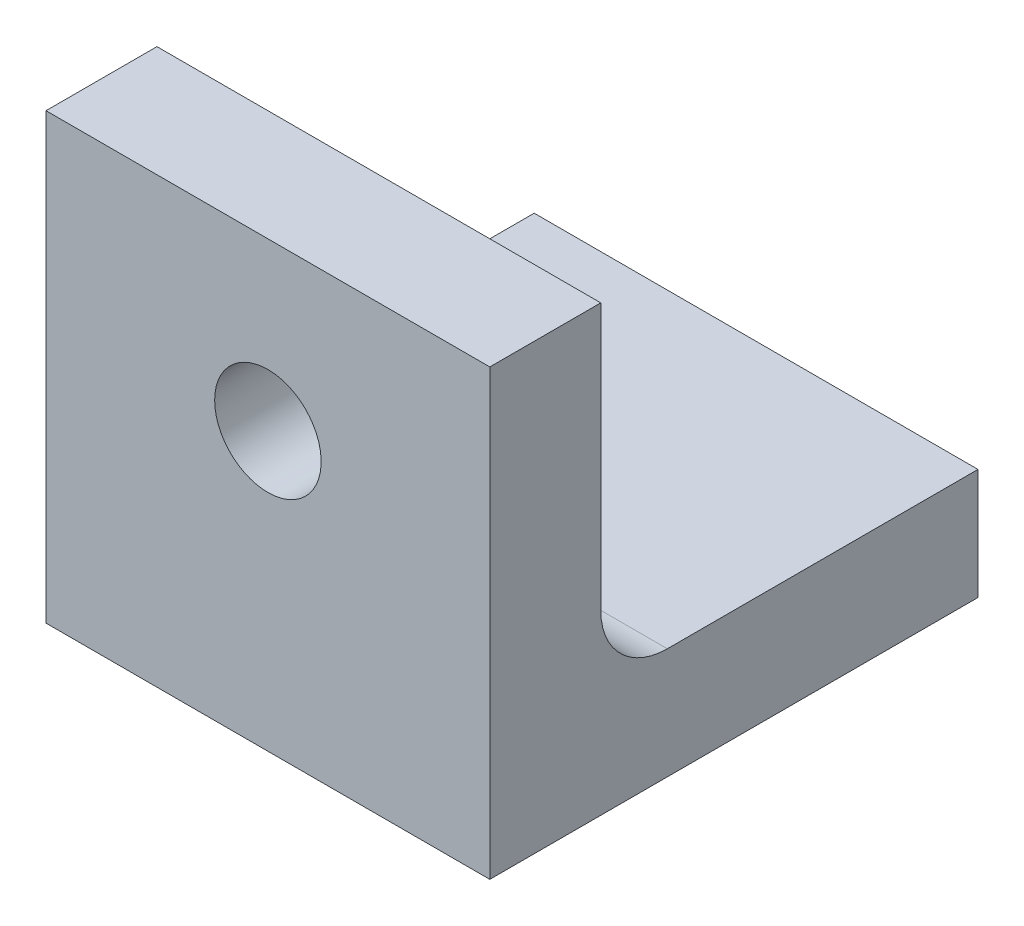
SolidWorks part; units mm, degrees
ref_plane "Front Plane" through (0, 0, 0) normal (0, 0, 1) x (1, 0, 0)
ref_plane "Top Plane" through (0, 0, 0) normal (0, 1, 0) x (1, 0, 0)
ref_plane "Right Plane" through (0, 0, 0) normal (1, 0, 0) x (0, 0, -1)
sketch "Sketch1" plane through (0, 0, 0) normal (0, 1, 0) x (1, 0, 0)
  line L0 (-10, 6) -> (10, 6)
  line L1 (-10, 11) -> (10, 11)
  line L2 (-10, 11) -> (-10, -11)
  line L3 (-10, -11) -> (10, -11)
  line L4 (10, 11) -> (10, -11)
  line L5 (-10, 11) -> (10, -11) construction
  line L6 (-10, -11) -> (10, 11) construction
  line L7 (-10, -6) -> (10, -6)
  point P0 (0, 0)
  dimension "D1" = 20
  dimension "D2" = 22
  dimension "D3" = 5
  dimension "D4" = 5
extrude "Boss-Extrude1" add sketch "Sketch1" along normal blind 5 contours L4 L1 L2 L0 | L2 L7 L4 L0 | L7 L2 L3 L4
sketch "Sketch2" plane through (0, 0, 11) normal (0, 0, 1) x (1, 0, 0)
  line L2 (10, 5) -> (-10, 5)
  line L3 (-10, 5) -> (-10, 0) construction
  line L5 (10, 5) -> (10, 20)
  line L6 (10, 20) -> (-10, 20)
  line L7 (-10, 5) -> (-10, 20)
  line L8 (-10, 5) -> (10, 5) construction
  point P1 (0, 0)
  point P9 (0, 0)
  point P10 (-10, 9.3459)
  dimension "D1" = 15
extrude "Boss-Extrude2" add sketch "Sketch2" along a picked direction on the side against the normal blind 5
hole_wizard "Ø5.0 (5) Diameter Hole1" positions "Sketch3" profile "Sketch4" hole size "Ø5.0" standard "ANSI Metric" end condition up to next
sketch "Sketch3" plane through (0, 5, 0) normal (0, 1, 0) x (1, 0, 0)
  point P0 (0, 0)
sketch "Sketch4" plane through (0, 5, 0) normal (1, 0, 0) x (0, 0, 1)
  line L0 (0, 0) -> (0, 5)
  line L1 (0, 5) -> (2.5, 5)
  line L2 (2.5, 5) -> (2.5, 0)
  line L5 (2.5, 0) -> (0, 0)
  line L11 (0, -6.35) -> (0, 107.95) construction
  dimension "Thru Hole Dia." = 5
  dimension "Thru Hole Depth" = 5
sketch "Sketch7" plane through (0, 0, 6) normal (0, 0, 1) x (1, 0, 0)
  line L3 (10, 5) -> (10, 20) construction
  line L4 (10, 20) -> (-10, 20) construction
  point P0 (0, 12.5)
  point P8 (0, 0)
  point P10 (10, 17.0161)
  point P11 (10, 14.4031)
  point P12 (0, 0)
  point P13 (0, 0)
  point P14 (10, 0)
  point P16 (10, 20)
  point P21 (10, 12.5)
  point P24 (0, 20)
hole_wizard "Ø4.5 M4 heat set" positions "Sketch7" profile "Sketch8" hole size "Ø4.8" standard "ANSI Metric" end condition up to next
sketch "Sketch8" plane through (0, 12.5, 6) normal (1, 0, 0) x (0, 1, 0)
  line L0 (0, 0) -> (0, 5)
  line L1 (0, 5) -> (2.4, 5)
  line L2 (2.4, 5) -> (2.4, 0)
  line L5 (2.4, 0) -> (0, 0)
  line L11 (0, -6.35) -> (0, 107.95) construction
  dimension "Thru Hole Dia." = 4.8
  dimension "Thru Hole Depth" = 5
fillet "Fillet1" radius 3 1 edges at (0, 5, 6)
